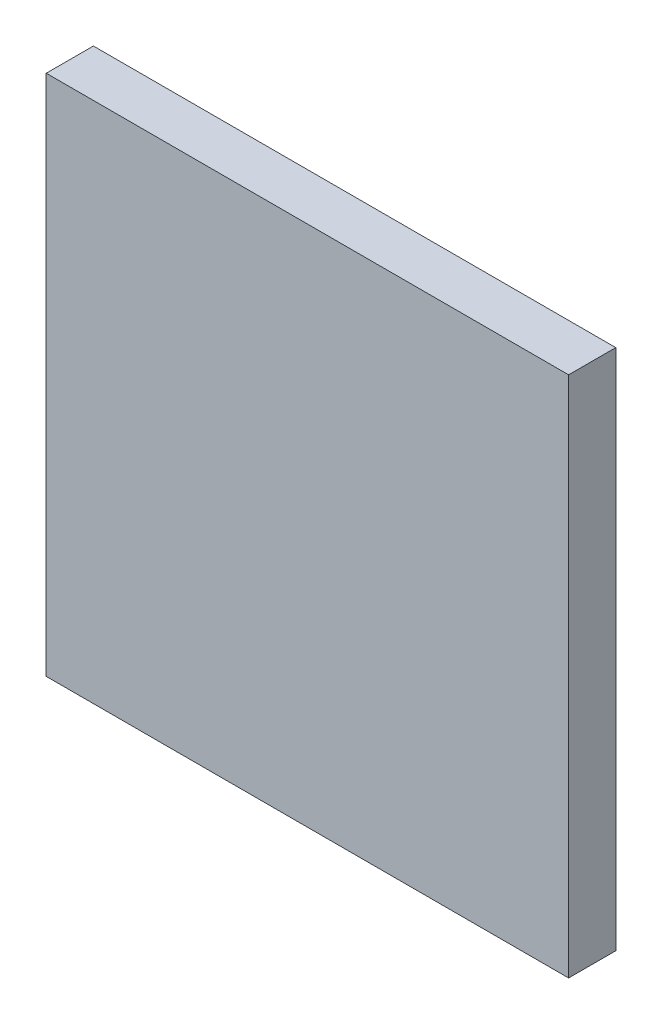
SolidWorks part; units mm, degrees
ref_plane "Front Plane" through (0, 0, 0) normal (0, 0, 1) x (1, 0, 0)
ref_plane "Top Plane" through (0, 0, 0) normal (0, 1, 0) x (1, 0, 0)
ref_plane "Right Plane" through (0, 0, 0) normal (1, 0, 0) x (0, 0, -1)
sketch "Sketch17" plane through (0, 0, 0) normal (0, 0, 1) x (1, 0, 0)
  line L1 (0, 27.7) -> (27.7, 27.7)
  line L2 (0, 27.7) -> (0, 0)
  line L3 (0, 0) -> (27.7, 0)
  line L4 (27.7, 27.7) -> (27.7, 0)
extrude "filter" add sketch "Sketch17" along normal blind 2.5 separate body
